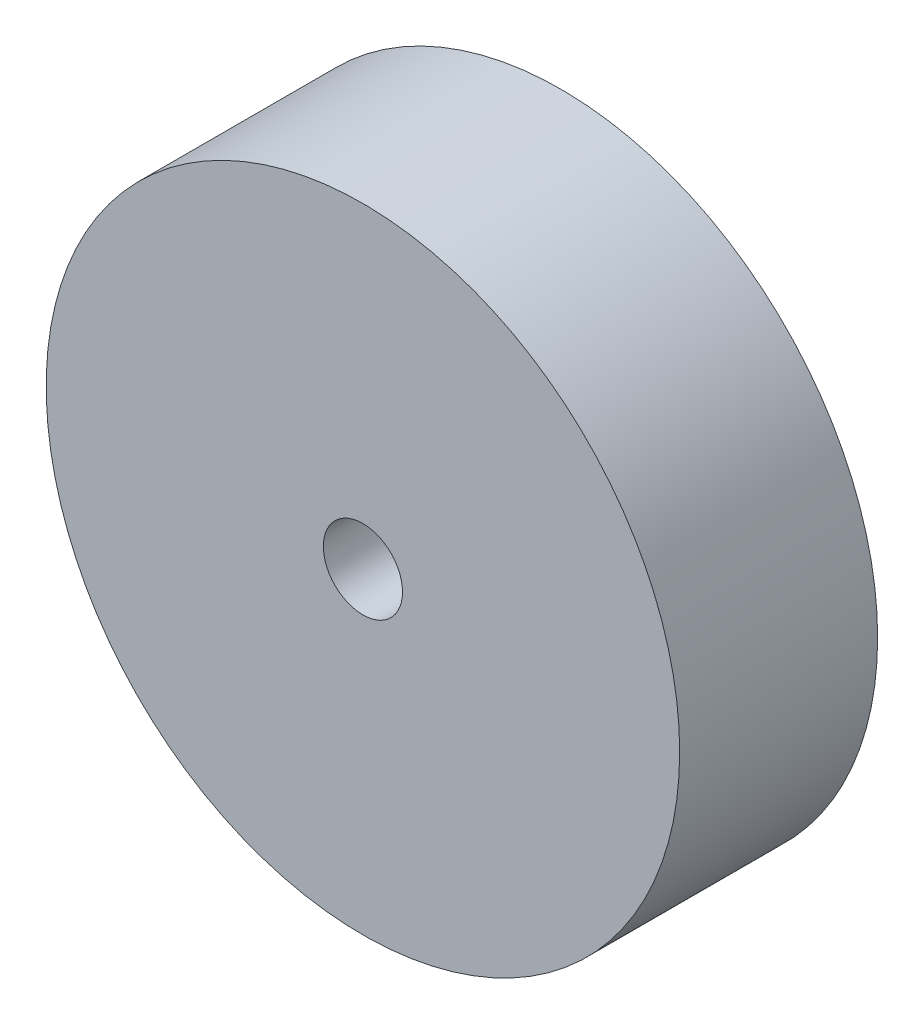
SolidWorks part; units mm, degrees
ref_plane "Front Plane" through (0, 0, 0) normal (0, 0, 1) x (1, 0, 0)
ref_plane "Top Plane" through (0, 0, 0) normal (0, 1, 0) x (1, 0, 0)
ref_plane "Right Plane" through (0, 0, 0) normal (1, 0, 0) x (0, 0, -1)
sketch "Sketch1" plane through (0, 0, 0) normal (0, 0, 1) x (1, 0, 0)
  circle A0 centre (0, 0) radius 6.35
  circle A1 centre (0, 0) radius 50.8
  dimension "D1" = 101.6
  dimension "D2" = 12.7
extrude "Boss-Extrude1" add sketch "Sketch1" along normal blind 31.75
